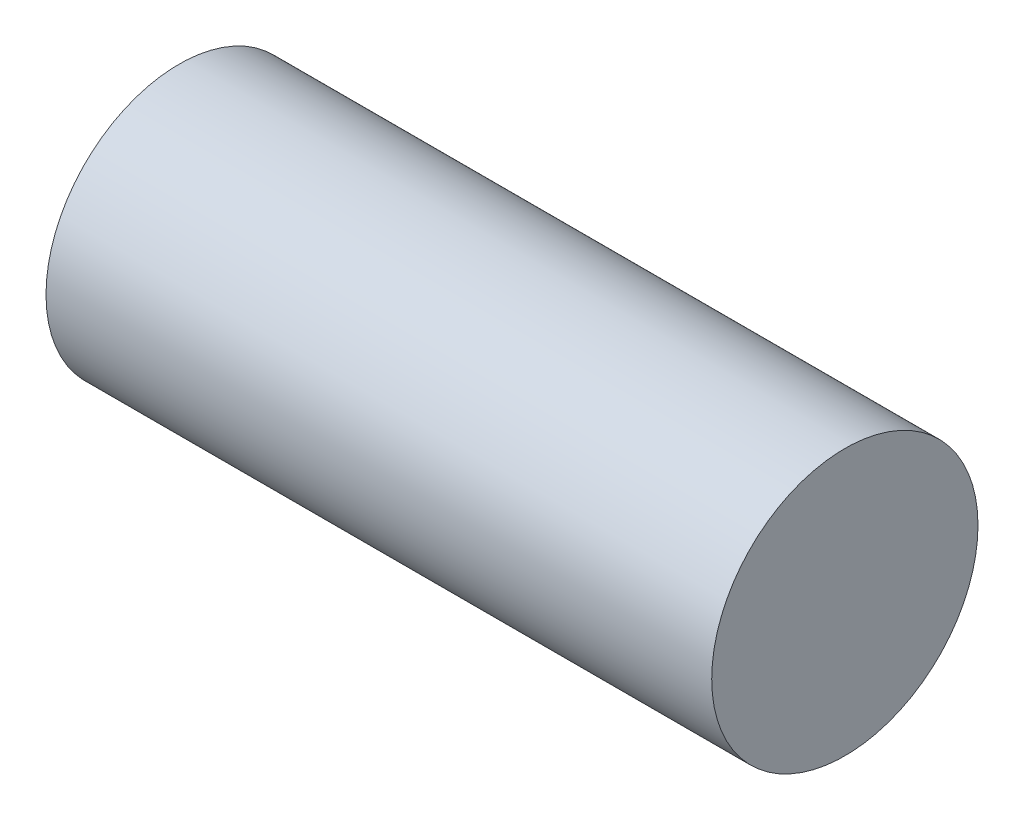
SolidWorks part; units mm, degrees
material "Ti-5Al-2.5Sn Annealed (SS)"
ref_plane "Front Plane" through (0, 0, 0) normal (0, 0, 1) x (1, 0, 0)
ref_plane "Top Plane" through (0, 0, 0) normal (0, 1, 0) x (1, 0, 0)
ref_plane "Right Plane" through (0, 0, 0) normal (1, 0, 0) x (0, 0, -1)
sketch "RivetProfile" plane through (0, 0, 0) normal (1, 0, 0) x (0, 0, -1)
  circle A0 centre (0, 0) radius 40
  dimension "D1" = 80
extrude "Boss-Extrude1" add sketch "RivetProfile" along normal blind 200 contours A0
equation "\"D1@RivetProfile\" = \"HoleMountDiameter@PrintingPress.Assembly\""
equation "\"D1@Boss-Extrude1\"=2*\"RivetLength@PrintingPress.Assembly\""
